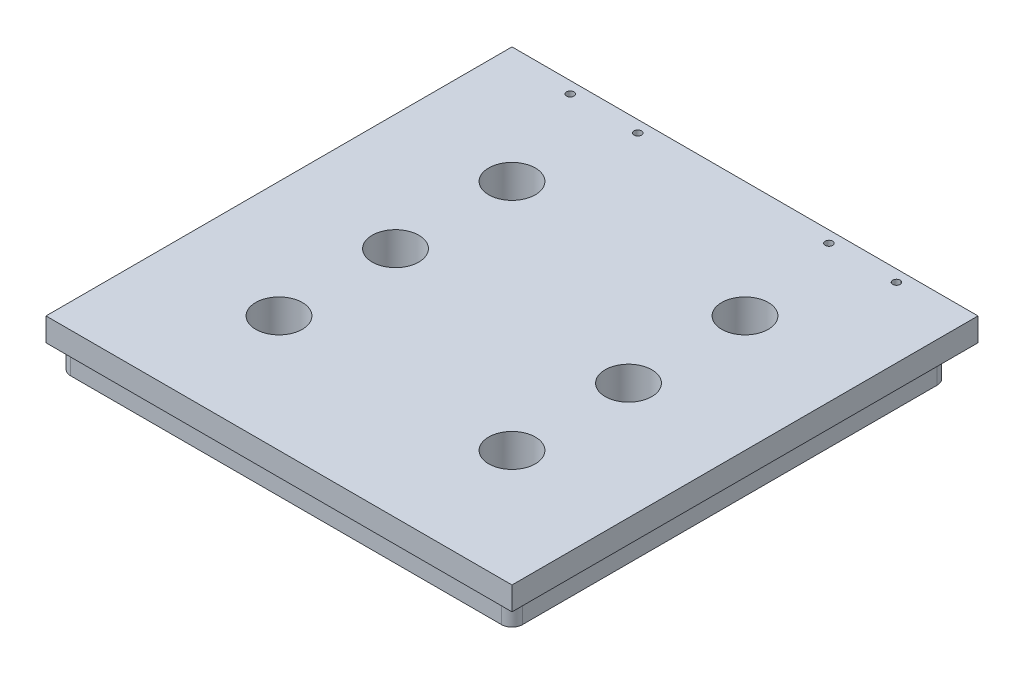
SolidWorks part; units mm, degrees
ref_plane "Alzado" through (0, 0, 0) normal (0, 0, 1) x (1, 0, 0)
ref_plane "Planta" through (0, 0, 0) normal (0, 1, 0) x (1, 0, 0)
ref_plane "Vista lateral" through (0, 0, 0) normal (1, 0, 0) x (0, 0, -1)
sketch "Croquis1" plane through (0, 0, 0) normal (0, 1, 0) x (1, 0, 0)
  line L1 (100, -100) -> (-100, -100)
  line L2 (100, -100) -> (100, 100)
  line L3 (100, 100) -> (-100, 100)
  line L4 (-100, -100) -> (-100, 100)
  line L5 (100, -100) -> (-100, 100) construction
  line L6 (100, 100) -> (-100, -100) construction
  point P0 (0, 0)
  dimension "D1" = 200
  dimension "D2" = 200
extrude "Saliente-Extruir1" add sketch "Croquis1" along normal blind 10
sketch "Croquis2" plane through (0, 0, 0) normal (0, -1, 0) x (1, 0, 0)
  line L0 (-100, 100) -> (100, 100) construction
  line L1 (-97, 97) -> (97, 97)
  line L2 (-97, 97) -> (-97, -90)
  line L3 (-97, -90) -> (97, -90)
  line L4 (97, 97) -> (97, -90)
  line L5 (-97, 97) -> (97, -90) construction
  line L6 (-97, -90) -> (97, 97) construction
  line L7 (-100, -100) -> (-100, 100) construction
  line L8 (100, -100) -> (-100, -100) construction
  line L9 (100, 100) -> (100, -100) construction
  point P4 (0, 3.5)
  dimension "D1" = 3
  dimension "D2" = 3
  dimension "D3" = 10
  dimension "D4" = 3
extrude "Saliente-Extruir2" add sketch "Croquis2" along normal blind 10
fillet "Redondeo2" radius 4.5 4 edges at (97, -5, 97) (-97, -5, 97) (-97, -5, -90) (97, -5, -90)
sketch "Croquis3" plane through (0, 10, 0) normal (0, 1, 0) x (1, 0, 0)
  line L0 (-100, -100) -> (100, -100) construction
  line L1 (100, 100) -> (-100, 100) construction
  line L2 (-100, 100) -> (-100, -100) construction
  circle A0 centre (-50, 50) radius 10
  circle A1 centre (-50, 0) radius 10
  circle A2 centre (-50, -50) radius 10
  dimension "D1" = 20
  dimension "D2" = 20
  dimension "D3" = 20
  dimension "D4" = 50
  dimension "D5" = 50
  dimension "D6" = 50
  dimension "D7" = 50
  dimension "D8" = 50
  dimension "D9" = 50
  dimension "D10" = 50
extrude "Cortar-Extruir1" cut sketch "Croquis3" against normal up to next (20 mm away)
mirror "Simetría1" about plane through (0, 0, 0) normal (1, 0, 0) of "Cortar-Extruir1"
sketch "Croquis4" plane through (0, 10, 0) normal (0, 1, 0) x (1, 0, 0)
  line L1 (100, 100) -> (-100, 100) construction
  line L2 (-100, 100) -> (-100, -100) construction
  circle A0 centre (-70, 95) radius 1.6
  circle A1 centre (-41, 95) radius 1.6
  dimension "D1" = 3.2
  dimension "D2" = 3.2
  dimension "D3" = 29
  dimension "D4" = 5
  dimension "D5" = 5
  dimension "D6" = 30
extrude "Cortar-Extruir2" cut sketch "Croquis4" against normal up to next (10 mm away)
mirror "Simetría2" about plane through (0, 0, 0) normal (1, 0, 0) of "Cortar-Extruir2"
